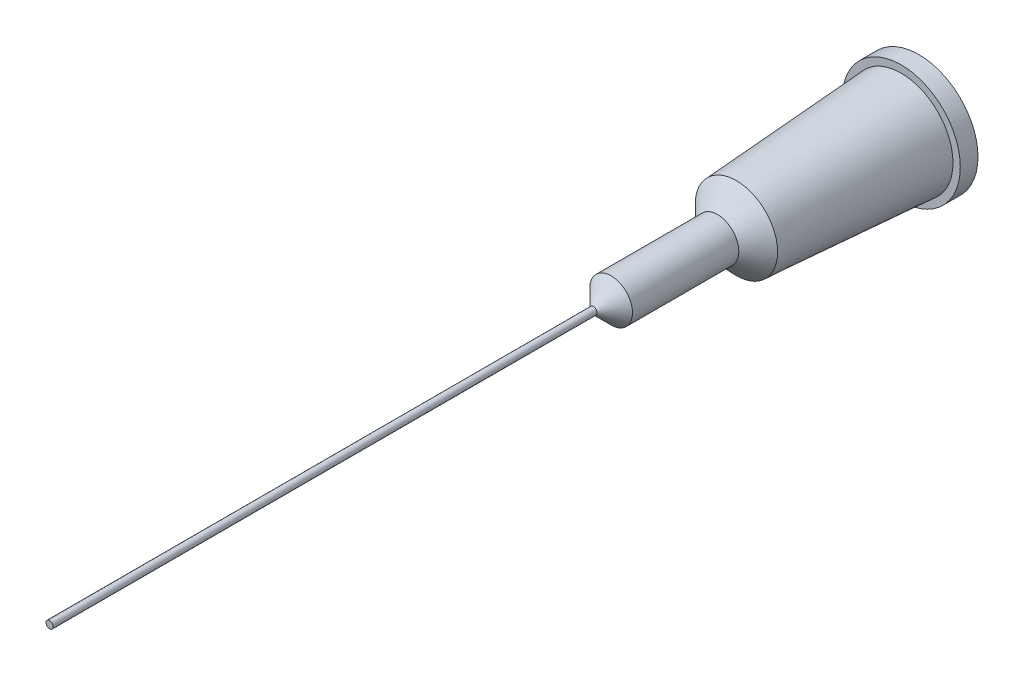
SolidWorks part; units mm, degrees
ref_plane "Front Plane" through (0, 0, 0) normal (0, 0, 1) x (1, 0, 0)
ref_plane "Top Plane" through (0, 0, 0) normal (0, 1, 0) x (1, 0, 0)
ref_plane "Right Plane" through (0, 0, 0) normal (1, 0, 0) x (0, 0, -1)
sketch "Sketch1" plane through (0, 0, 0) normal (0, 1, 0) x (1, 0, 0)
  line L0 (-3.335, 0) -> (-3.335, -1)
  line L1 (-3.335, -1) -> (-2.925, -1)
  line L2 (-2.325, -10.3) -> (-1.205, -11.37)
  line L3 (-1.205, -11.37) -> (-1.205, -17.37)
  line L4 (-1.205, -17.37) -> (-0.205, -18.37)
  line L5 (-0.205, -18.37) -> (-0.205, -49.06)
  line L6 (-0.205, -49.06) -> (0, -49.06)
  line L7 (0, -49.06) -> (0, 0)
  line L8 (0, 0) -> (-3.335, 0)
  line L9 (-2.925, -1) -> (-2.325, -10.3)
  dimension "D1" = 3.335
  dimension "D2" = 1
  dimension "D3" = 0.41
  dimension "D4" = 10.3
  dimension "D5" = 18.37
  dimension "D6" = 1
  dimension "D7" = 7
  dimension "D8" = 45
  dimension "D9" = 0.205
  dimension "D10" = 49.06
  dimension "D11" = 1.12
revolve "Revolve1" add sketch "Sketch1" angle 360 about L7
